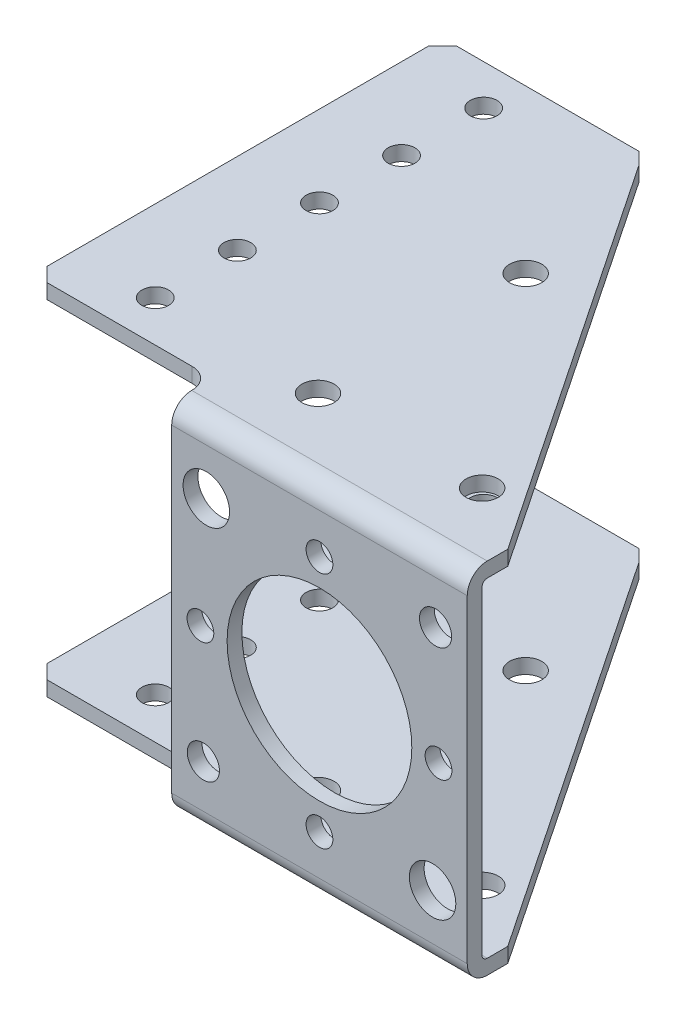
SolidWorks part; units mm, degrees
ref_plane "Front Plane" through (0, 0, 0) normal (0, 0, 1) x (1, 0, 0)
ref_plane "Top Plane" through (0, 0, 0) normal (0, 1, 0) x (1, 0, 0)
ref_plane "Right Plane" through (0, 0, 0) normal (1, 0, 0) x (0, 0, -1)
ref_plane "Plane1" through (0, 0, 2.286) normal (0, 0, 1) x (1, 0, 0)
sketch "Sketch1" plane through (0, 0, 2.286) normal (0, 0, 1) x (1, 0, 0)
  line L0 (-19.685, -25.4635) -> (22.86, -25.4635)
  line L1 (22.86, -25.4635) -> (22.86, 25.4635)
  line L2 (22.86, 25.4635) -> (-19.685, 25.4635)
  line L3 (-19.685, 25.4635) -> (-19.685, -25.4635)
extrude "Boss-Extrude1" add sketch "Sketch1" against normal blind 6.2738
sketch "Sketch2" plane through (0, -25.4635, 0) normal (0, -1, 0) x (1, 0, 0)
  line L0 (-19.685, 2.286) -> (22.86, 2.286)
  line L1 (22.86, 2.286) -> (22.86, -3.9878)
  line L2 (22.86, -3.9878) -> (-19.685, -67.437)
  line L3 (-19.685, -67.437) -> (-19.685, 2.286)
extrude "Boss-Extrude2" add sketch "Sketch2" along normal blind 2.286
sketch "Sketch3" plane through (0, 25.4635, 0) normal (0, 1, 0) x (-1, 0, 0)
  line L0 (19.685, -67.437) -> (-22.86, -3.9878)
  line L1 (-22.86, -3.9878) -> (-22.86, 2.286)
  line L2 (-22.86, 2.286) -> (19.685, 2.286)
  line L3 (19.685, 2.286) -> (19.685, -67.437)
extrude "Boss-Extrude3" add sketch "Sketch3" along normal blind 2.286
sketch "Sketch4" plane through (0, 0, -3.9878) normal (0, 0, -1) x (-1, 0, 0)
  line L0 (-22.86, -25.4635) -> (19.685, -25.4635)
  line L1 (19.685, -25.4635) -> (19.685, 25.4635)
  line L2 (19.685, 25.4635) -> (-22.86, 25.4635)
  line L3 (-22.86, 25.4635) -> (-22.86, -25.4635)
extrude "Cut-Extrude1" cut sketch "Sketch4" against normal blind 3.9878
sketch "Sketch5" plane through (-19.685, 0, 0) normal (-1, 0, 0) x (0, 0, 1)
  line L0 (0, -25.4635) -> (0, 25.4635)
  line L1 (0, 25.4635) -> (-67.437, 25.4635)
  line L2 (-67.437, 25.4635) -> (-67.437, 27.7495)
  line L3 (-67.437, 27.7495) -> (2.286, 27.7495)
  line L4 (2.286, 27.7495) -> (2.286, -27.7495)
  line L5 (2.286, -27.7495) -> (-67.437, -27.7495)
  line L6 (-67.437, -27.7495) -> (-67.437, -25.4635)
  line L7 (-67.437, -25.4635) -> (0, -25.4635)
extrude "Boss-Extrude4" add sketch "Sketch5" along normal blind 3.175
sketch "Sketch6" plane through (-22.86, 0, 0) normal (-1, 0, 0) x (0, 0, 1)
  line L0 (-4.064, 25.4635) -> (-67.437, 25.4635)
  line L1 (-67.437, 25.4635) -> (-67.437, 27.7495)
  line L2 (-67.437, 27.7495) -> (-4.064, 27.7495)
  line L3 (-4.064, 27.7495) -> (-4.064, 25.4635)
extrude "Boss-Extrude5" add sketch "Sketch6" along normal blind 27.813
sketch "Sketch7" plane through (-22.86, 0, 0) normal (-1, 0, 0) x (0, 0, 1)
  line L0 (-4.064, -27.7495) -> (-67.437, -27.7495)
  line L1 (-67.437, -27.7495) -> (-67.437, -25.4635)
  line L2 (-67.437, -25.4635) -> (-4.064, -25.4635)
  line L3 (-4.064, -25.4635) -> (-4.064, -27.7495)
extrude "Boss-Extrude6" add sketch "Sketch7" along normal blind 27.813
hole_wizard "Hole1" positions "Sketch9" profile "Sketch8" legacy
sketch "Sketch9" plane through (0, -25.4635, 0) normal (0, 1, 0) x (1, 0, 0)
  point P0 (-12.7, 10.1854)
  point P1 (12.7, 10.1854)
  point P2 (-12.7, 42.3164)
sketch "Sketch8" plane through (-12.7, -25.4635, -10.1854) normal (1, 0, 0) x (0, 0, 1)
  line L0 (0, 0) -> (0, 2.286)
  line L1 (0, 2.286) -> (2.4892, 2.286)
  line L2 (2.4892, 2.286) -> (2.4892, 0)
  line L3 (2.4892, 0) -> (0, 0)
  line L4 (0, 110) -> (0, -10) construction
  dimension "Diameter" = 4.9784
  dimension "Depth" = 2.286
hole_wizard "M3.5 Clearance Hole1" positions "Sketch11" profile "Sketch10" hole size "M3.5" standard "ANSI Metric"
sketch "Sketch11" plane through (0, -25.4635, 0) normal (0, 1, 0) x (1, 0, 0)
  point P0 (-38.1, 61.214)
  point P1 (-38.1, 48.514)
  point P2 (-38.1, 35.814)
  point P3 (-38.1, 23.114)
  point P4 (-38.1, 10.414)
sketch "Sketch10" plane through (-38.1, -25.4635, -61.214) normal (1, 0, 0) x (0, 0, 1)
  line L0 (0, 0) -> (0, 2.286)
  line L1 (0, 2.286) -> (2.0701, 2.286)
  line L2 (2.0701, 2.286) -> (2.0701, 0)
  line L5 (2.0701, 0) -> (0, 0)
  line L11 (0, -6.35) -> (0, 107.95) construction
  dimension "Thru Hole Dia." = 4.1402
  dimension "Thru Hole Depth" = 2.286
hole_wizard "M25 Clearance Hole1" positions "Sketch13" profile "Sketch12" hole size "M25" standard "ANSI Metric"
sketch "Sketch13" plane through (0, 0, 0) normal (0, 0, -1) x (-1, 0, 0)
  point P0 (0, 0)
sketch "Sketch12" plane through (0, 0, 0) normal (1, 0, 0) x (0, 1, 0)
  line L0 (0, 0) -> (0, 2.286)
  line L1 (0, 2.286) -> (14.2875, 2.286)
  line L2 (14.2875, 2.286) -> (14.2875, 0)
  line L5 (14.2875, 0) -> (0, 0)
  line L11 (0, -6.35) -> (0, 107.95) construction
  dimension "Thru Hole Dia." = 28.575
  dimension "Thru Hole Depth" = 2.286
hole_wizard "Hole2" positions "Sketch15" profile "Sketch14" legacy
sketch "Sketch15" plane through (0, 0, 0) normal (0, 0, -1) x (-1, 0, 0)
  point P0 (-17.9605, 17.9605)
  point P1 (17.9605, -17.9605)
sketch "Sketch14" plane through (17.9605, 17.9605, 0) normal (1, 0, 0) x (0, 1, 0)
  line L0 (0, 0) -> (0, 2.286)
  line L1 (0, 2.286) -> (2.4892, 2.286)
  line L2 (2.4892, 2.286) -> (2.4892, 0)
  line L3 (2.4892, 0) -> (0, 0)
  line L4 (0, 110) -> (0, -10) construction
  dimension "Diameter" = 4.9784
  dimension "Depth" = 2.286
hole_wizard "M6.5 Clearance Hole1" positions "Sketch17" profile "Sketch16" hole size "M6.5" standard "ANSI Metric"
sketch "Sketch17" plane through (0, 0, 0) normal (0, 0, -1) x (-1, 0, 0)
  point P0 (17.5, 17.5)
  point P1 (-17.5, -17.5)
sketch "Sketch16" plane through (-17.5, 17.5, 0) normal (1, 0, 0) x (0, 1, 0)
  line L0 (0, 0) -> (0, 2.286)
  line L1 (0, 2.286) -> (3.5941, 2.286)
  line L2 (3.5941, 2.286) -> (3.5941, 0)
  line L5 (3.5941, 0) -> (0, 0)
  line L11 (0, -6.35) -> (0, 107.95) construction
  dimension "Thru Hole Dia." = 7.1882
  dimension "Thru Hole Depth" = 2.286
hole_wizard "M3.5 Clearance Hole2" positions "Sketch19" profile "Sketch18" hole size "M3.5" standard "ANSI Metric"
sketch "Sketch19" plane through (0, 0, 0) normal (0, 0, -1) x (-1, 0, 0)
  point P0 (18.415, 0)
  point P1 (0, 18.415)
  point P2 (0, -18.415)
  point P3 (-18.415, 0)
sketch "Sketch18" plane through (-18.415, 0, 0) normal (1, 0, 0) x (0, 1, 0)
  line L0 (0, 0) -> (0, 2.286)
  line L1 (0, 2.286) -> (2.0701, 2.286)
  line L2 (2.0701, 2.286) -> (2.0701, 0)
  line L5 (2.0701, 0) -> (0, 0)
  line L11 (0, -6.35) -> (0, 107.95) construction
  dimension "Thru Hole Dia." = 4.1402
  dimension "Thru Hole Depth" = 2.286
hole_wizard "Hole3" positions "Sketch21" profile "Sketch20" legacy
sketch "Sketch21" plane through (0, 27.7495, 0) normal (0, 1, 0) x (1, 0, 0)
  point P0 (-12.7, 10.1854)
  point P1 (12.7, 10.1854)
  point P2 (-12.7, 42.3164)
sketch "Sketch20" plane through (-12.7, 27.7495, -10.1854) normal (1, 0, 0) x (0, 0, 1)
  line L0 (0, 0) -> (0, 55.499)
  line L1 (0, 55.499) -> (2.4892, 55.499)
  line L2 (2.4892, 55.499) -> (2.4892, 0)
  line L3 (2.4892, 0) -> (0, 0)
  line L4 (0, 110) -> (0, -10) construction
  dimension "Diameter" = 4.9784
  dimension "Depth" = 55.499
hole_wizard "M3.5 Clearance Hole3" positions "Sketch23" profile "Sketch22" hole size "M3.5" standard "ANSI Metric"
sketch "Sketch23" plane through (0, 27.7495, 0) normal (0, 1, 0) x (1, 0, 0)
  point P0 (-38.1, 61.214)
  point P1 (-38.1, 48.514)
  point P2 (-38.1, 35.814)
  point P3 (-38.1, 23.114)
  point P4 (-38.1, 10.414)
sketch "Sketch22" plane through (-38.1, 27.7495, -61.214) normal (1, 0, 0) x (0, 0, 1)
  line L0 (0, 0) -> (0, 55.499)
  line L1 (0, 55.499) -> (2.0701, 55.499)
  line L2 (2.0701, 55.499) -> (2.0701, 0)
  line L5 (2.0701, 0) -> (0, 0)
  line L11 (0, -6.35) -> (0, 107.95) construction
  dimension "Thru Hole Dia." = 4.1402
  dimension "Thru Hole Depth" = 55.499
chamfer "Chamfer1" distance 2.159 angle 11.157 1 edges at (-19.685, -26.6065, -67.437)
chamfer "Chamfer2" distance 2.159 angle 45 4 edges at (-50.673, -26.6065, -67.437) (-50.673, 26.6065, -67.437) (-50.673, -26.6065, -4.064) (-50.673, 26.6065, -4.064)
chamfer "Chamfer3" distance 0.5908 angle 45 1 edges at (-19.685, 26.6065, -67.437)
fillet "Fillet1" radius 0.8128 2 edges at (0, 25.4635, 0) (0, -25.4635, 0)
fillet "Fillet2" radius 3.0988 2 edges at (0, 27.7495, 2.286) (0, -27.7495, 2.286)
fillet "Fillet3" radius 3.2004 2 edges at (-22.86, -26.6065, -4.064)
